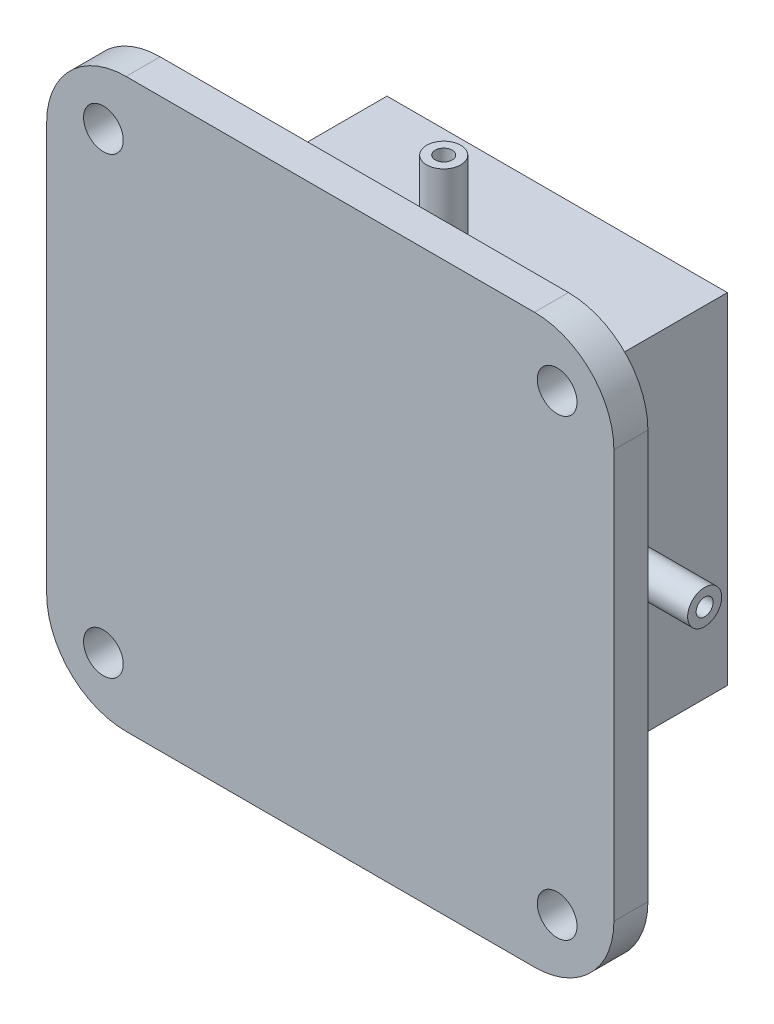
SolidWorks part; units mm, degrees
ref_plane "前视基准面" through (0, 0, 0) normal (0, 0, 1) x (1, 0, 0)
ref_plane "上视基准面" through (0, 0, 0) normal (0, 1, 0) x (1, 0, 0)
ref_plane "右视基准面" through (0, 0, 0) normal (1, 0, 0) x (0, 0, -1)
other "Configuration Table"
sketch "草图1" plane through (0, 0, 0) normal (0, 0, 1) x (1, 0, 0)
  line L1 (-18, -25) -> (18, -25)
  line L2 (-25, -18) -> (-25, 18)
  line L3 (-18, 25) -> (18, 25)
  line L4 (25, -18) -> (25, 18)
  line L5 (-25, -25) -> (25, 25) construction
  line L6 (-25, 25) -> (25, -25) construction
  circle A0 centre (20, 20) radius 1.75
  circle A1 centre (-20, 20) radius 1.75
  circle A2 centre (-20, -20) radius 1.75
  circle A3 centre (20, -20) radius 1.75
  arc A4 (18, -25) -> (25, -18) centre (18, -18) ccw
  arc A5 (-18, -25) -> (-25, -18) centre (-18, -18) cw
  arc A6 (18, 25) -> (25, 18) centre (18, 18) cw
  arc A7 (-25, 18) -> (-18, 25) centre (-18, 18) cw
  point P0 (0, 0)
  point P6 (20, 20)
  dimension "D3" = 5
  dimension "D6" = 3.5
  dimension "D7" = 3.5
  dimension "D4" = 3.5
  dimension "D8" = 3.5
  dimension "D11" = 7
  dimension "D1" = 50
  dimension "D2" = 50
  dimension "D5" = 5
  dimension "D9" = 5
  dimension "D10" = 5
extrude "凸台-拉伸3" add sketch "草图1" along normal blind 3 contours L2 A7 L3 A6 L4 A4 L1 A5 | A1 | A0 | A3 | A2
sketch "草图2" plane through (0, 0, 0) normal (0, 0, 1) x (1, 0, 0)
  line L1 (-15, 15) -> (15, 15)
  line L2 (-15, 15) -> (-15, -15)
  line L3 (-15, -15) -> (15, -15)
  line L4 (15, 15) -> (15, -15)
  line L5 (-15, 15) -> (15, -15) construction
  line L6 (-15, -15) -> (15, 15) construction
  point P0 (0, 0)
  dimension "D1" = 30
  dimension "D2" = 30
extrude "凸台-拉伸4" add sketch "草图2" against normal blind 17
sketch "草图3" plane through (0, 0, -17) normal (0, 0, -1) x (-1, 0, 0)
  line L0 (-15, -15) -> (-15, 15) construction
  line L1 (15, -15) -> (-15, -15) construction
  circle A0 centre (0, 0) radius 0.85
  circle A1 centre (0, -7.5) radius 0.85
  circle A2 centre (-7.5, 0) radius 0.85
  circle A3 centre (0, 7.5) radius 0.85
  circle A4 centre (7.5, 0) radius 0.85
  circle A5 centre (-7.5, 0) radius 1.25
  circle A6 centre (0, -7.5) radius 1.25
  circle A7 centre (0, 7.5) radius 1.25
  circle A8 centre (7.5, 0) radius 1.25
  dimension "D1" = 1.7
  dimension "D2" = 1.7
  dimension "D4" = 4
  dimension "D7" = 7.5
  dimension "D9" = 2.5
  dimension "D10" = 2.5
  dimension "D11" = 2.5
  dimension "D12" = 2.5
  dimension "D3" = 7.5
  dimension "D5" = 7.5
  dimension "D6" = 7.5
  dimension "D8" = 30
sketch "草图4" plane through (-15, 0, 0) normal (-1, 0, 0) x (0, 0, 1)
  line L0 (0, 0) -> (-7, 0)
  line L1 (0, 15) -> (0, -15) construction
  circle A0 centre (-7, 0) radius 0.75
extrude "切除-拉伸4" cut sketch "草图4" against normal blind 9 contours A0
sketch "草图5" plane through (0, 15, 0) normal (0, 1, 0) x (1, 0, 0)
  line L0 (0, 0) -> (0, 7)
  line L1 (15, 0) -> (-15, 0) construction
  circle A0 centre (0, 7) radius 0.75
extrude "切除-拉伸5" cut sketch "草图5" against normal blind 9 contours A0
sketch "草图15" plane through (15, 0, 0) normal (1, 0, 0) x (0, 0, -1)
  point P0 (7, 0)
sketch "草图17" plane through (15, 0, 0) normal (1, 0, 0) x (0, 0, -1)
  line L0 (7, 0) -> (0, 0)
  line L1 (0, -15) -> (0, 15) construction
  circle A0 centre (7, 0) radius 0.75
  dimension "D1" = 1.5
extrude "切除-拉伸6" cut sketch "草图17" against normal blind 9 contours A0
sketch "草图19" plane through (0, -15, 0) normal (0, -1, 0) x (1, 0, 0)
  line L0 (0, -7) -> (0, 0)
  line L1 (-15, 0) -> (15, 0) construction
  circle A0 centre (0, -7) radius 0.75
  point P0 (0, -7)
  dimension "D1" = 1.5
extrude "切除-拉伸7" cut sketch "草图19" against normal blind 9 contours A0
sketch "草图6" plane through (-15, 0, 0) normal (-1, 0, 0) x (0, 0, 1)
  circle A0 centre (-7, 0) radius 1.5
  circle A3 centre (-7, 0) radius 0.75
extrude "凸台-拉伸7" add sketch "草图6" along normal blind 8
sketch "草图11" plane through (0, 0, 0) normal (0, 1, 0) x (1, 0, 0)
  line L0 (0, 0) -> (0, 37.5452) construction
pattern_circular "阵列(圆周)1" count 4 over 360 about axis through (0, 0, 0) along (0, 0, 1) of "凸台-拉伸7"
sketch "草图12" plane through (0, 0, -17) normal (0, 0, -1) x (-1, 0, 0)
  line L0 (-15, 15) -> (15, 15) construction
  line L1 (15, -15) -> (-15, -15)
  line L2 (15, -15) -> (15, 15)
  line L3 (15, 15) -> (-15, 15)
  line L4 (-15, -15) -> (-15, 15)
  line L5 (-15, -15) -> (-15, 15) construction
extrude "切除-拉伸8" cut sketch "草图3" against normal blind 11 contours A2 | A1 | A3 | A4
sketch "草图21" plane through (0, 0, -17) normal (0, 0, -1) x (-1, 0, 0)
  circle A0 centre (-7.5, 0) radius 1.25
  circle A1 centre (0, 7.5) radius 1.25
  circle A2 centre (7.5, 0) radius 1.25
  circle A3 centre (0, -7.5) radius 1.25
  point P13 (0, 0)
  circle M1 centre (-7.5, 0) radius 0.85
  circle M2 centre (0, -7.5) radius 0.85
  circle M3 centre (0, 7.5) radius 0.85
  circle M4 centre (7.5, 0) radius 0.85
  dimension "D1" = 2.5
extrude "凸台-拉伸8" add sketch "草图21" along normal blind 6 contours A0 M1 | A3 M2 | A2 M4 | A1 M3
